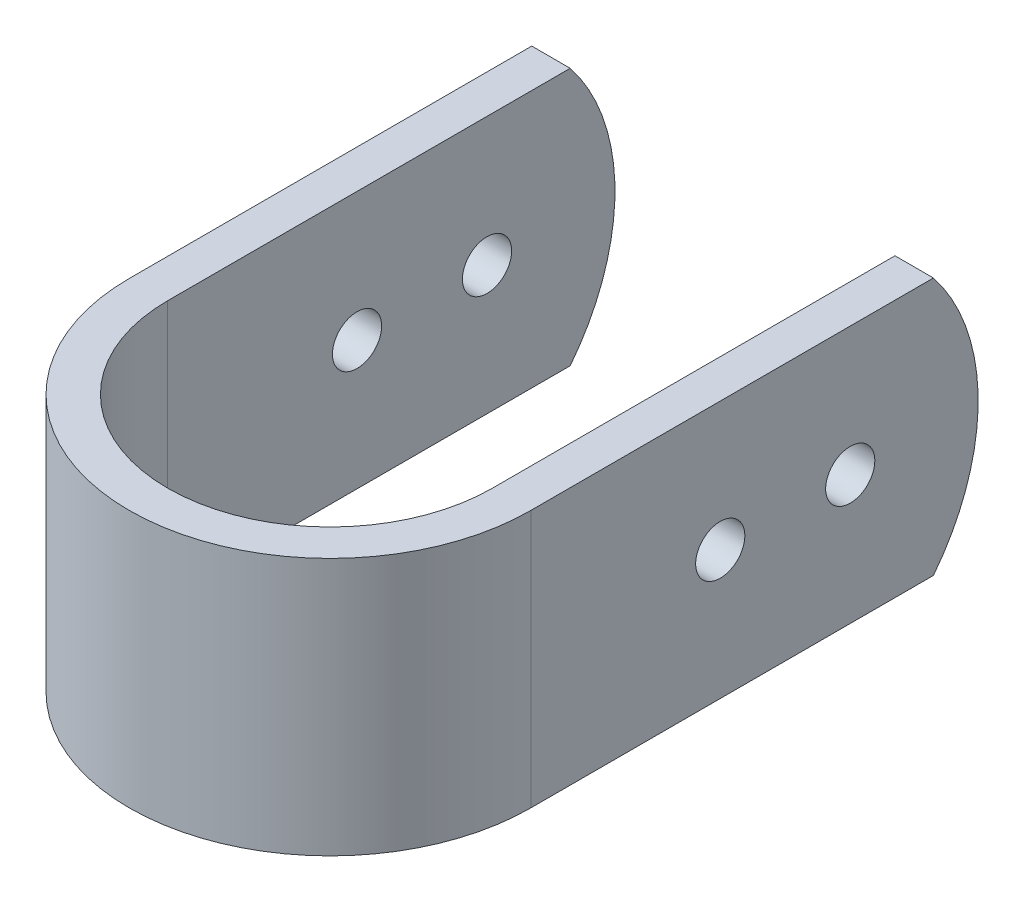
SolidWorks part; units mm, degrees
ref_plane "Front Plane" through (0, 0, 0) normal (0, 0, 1) x (1, 0, 0)
ref_plane "Top Plane" through (0, 0, 0) normal (0, 1, 0) x (1, 0, 0)
ref_plane "Right Plane" through (0, 0, 0) normal (1, 0, 0) x (0, 0, -1)
sketch "Sketch1" plane through (0, 0, 0) normal (0, 1, 0) x (1, 0, 0)
  line L0 (-22.45, 0) -> (-22.45, 50)
  line L1 (-22.45, 50) -> (-18.15, 50)
  line L2 (-18.15, 50) -> (-18.15, 0)
  line L3 (18.15, 0) -> (18.15, 50)
  line L4 (18.15, 50) -> (22.45, 50)
  line L5 (22.45, 50) -> (22.45, 0)
  line L6 (18.15, 0) -> (22.45, 0) construction
  line L7 (-22.45, 0) -> (-18.15, 0) construction
  line L8 (-18.15, 0) -> (0, 0) construction
  line L9 (0, 0) -> (18.15, 0) construction
  arc A0 (-22.45, 0) -> (22.45, 0) centre (0, 0) ccw
  arc A1 (-18.15, 0) -> (18.15, 0) centre (0, 0) ccw
  point P0 (-20.3, 50)
  dimension "D1" = 4.3
  dimension "D2" = 36.3
  dimension "D3" = 50
extrude "Boss-Extrude1" add sketch "Sketch1" along normal blind 28.8
sketch "Sketch2" plane through (22.45, 0, 0) normal (1, 0, 0) x (0, 0, -1)
  line L0 (0, 14.4) -> (50, 14.4) construction
  line L1 (0, 28.8) -> (0, 0) construction
  line L2 (50, 28.8) -> (50, 0) construction
  circle A0 centre (21.17, 14.4) radius 1
  circle A1 centre (35.7, 14.4) radius 1
  point P10 (12.3868, 14.4)
  point P11 (29.2767, 14.4)
  dimension "D3" = 2
  dimension "D4" = 2
  dimension "D1" = 14.3
  dimension "D2" = 14.53
hole_wizard "M5 Clearance Hole1" positions "Sketch3" profile "Sketch4" hole size "M5" standard "ANSI Metric" end condition through all
sketch "Sketch3" plane through (22.45, 0, 0) normal (1, 0, 0) x (0, 0, -1)
  point P0 (21.17, 14.4)
  point P3 (35.7, 14.4)
sketch "Sketch4" plane through (22.45, 14.4, -21.17) normal (0, 1, 0) x (0, 0, -1)
  line L0 (0, 0) -> (0, 44.9)
  line L1 (0, 44.9) -> (2.75, 44.9)
  line L2 (2.75, 44.9) -> (2.75, 0)
  line L5 (2.75, 0) -> (0, 0)
  line L11 (0, -6.35) -> (0, 107.95) construction
  dimension "Thru Hole Dia." = 5.5
  dimension "Thru Hole Depth" = 44.9
sketch "Sketch5" plane through (22.45, 0, 0) normal (1, 0, 0) x (0, 0, -1)
  line L0 (45, 28.8) -> (45, 0) construction
  line L1 (0, 28.8) -> (50, 28.8) construction
  line L2 (0, 0) -> (50, 0) construction
  line L3 (50, 28.8) -> (50, 0) construction
  line L4 (45, 28.8) -> (50, 28.8)
  line L5 (50, 28.8) -> (50, 0)
  line L6 (50, 0) -> (45, 0)
  arc A0 (45, 28.8) -> (45, 0) centre (26.764, 14.4) cw
  line M4 (0, 0) -> (50, 0)
  line M5 (50, 0) -> (50, 28.8)
  line M6 (50, 28.8) -> (0, 28.8)
  dimension "D1" = 5
extrude "Cut-Extrude1" cut sketch "Sketch5" against normal through all contours A0 M5 M4 | A0 L5 M6
